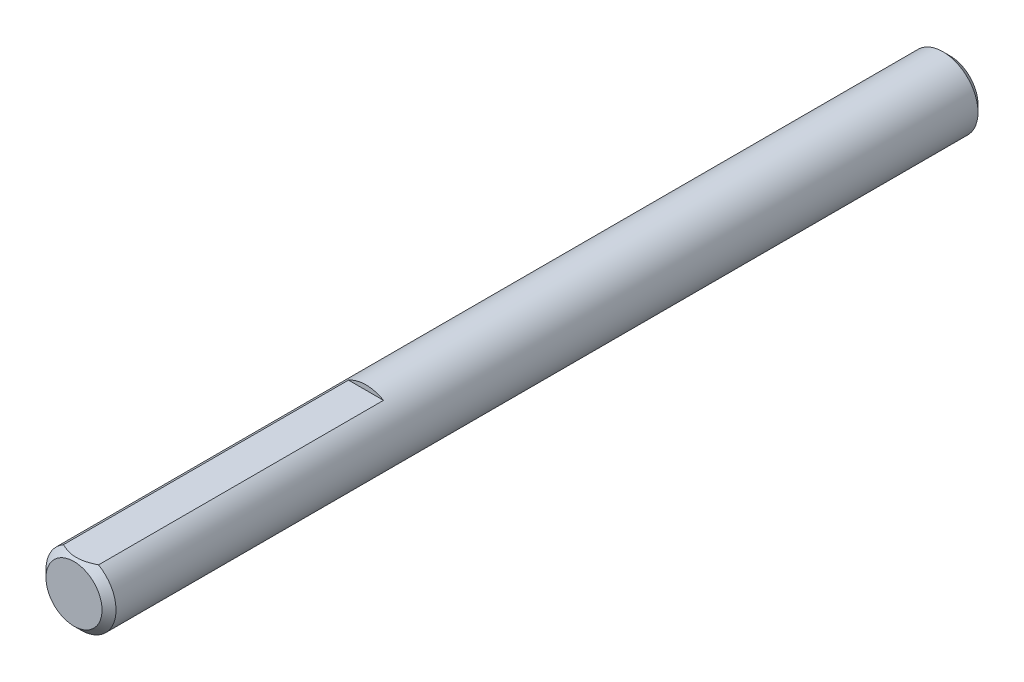
SolidWorks part; units mm, degrees
ref_plane "Front" through (0, 0, 0) normal (0, 0, 1) x (1, 0, 0)
ref_plane "Top" through (0, 0, 0) normal (0, 1, 0) x (1, 0, 0)
ref_plane "Right" through (0, 0, 0) normal (1, 0, 0) x (0, 0, -1)
sketch "Sketch1" plane through (0, 0, 0) normal (0, 0, 1) x (1, 0, 0)
  circle A0 centre (0, 0) radius 3.048
  dimension "D1" = 6.096
extrude "Extrude1" add sketch "Sketch1" along normal mid plane 76.2
chamfer "Chamfer1" distance 0.6096 angle 45 2 edges at (3.048, 0, -38.1) (3.048, 0, 38.1)
ref_plane "Plane1" through (0, 0, 12.7) normal (0, 0, 1) x (1, 0, 0)
sketch "Sketch13" plane through (0, 0, 12.7) normal (0, 0, 1) x (1, 0, 0)
  line L3 (-1.524, 2.6396) -> (1.524, 2.6396)
  circle A0 centre (0, 0) radius 3.048 construction
  arc A1 (1.524, 2.6396) -> (-1.524, 2.6396) centre (0, 0) ccw
  dimension "D1" = 3.048
extrude "Extrude7" cut sketch "Sketch13" along normal through all
equation "\"D1@Chamfer1\" = \"D1@Sketch1\" * .1"
equation "\"D1@Sketch13\" = \"D1@Sketch1\" * .5"
